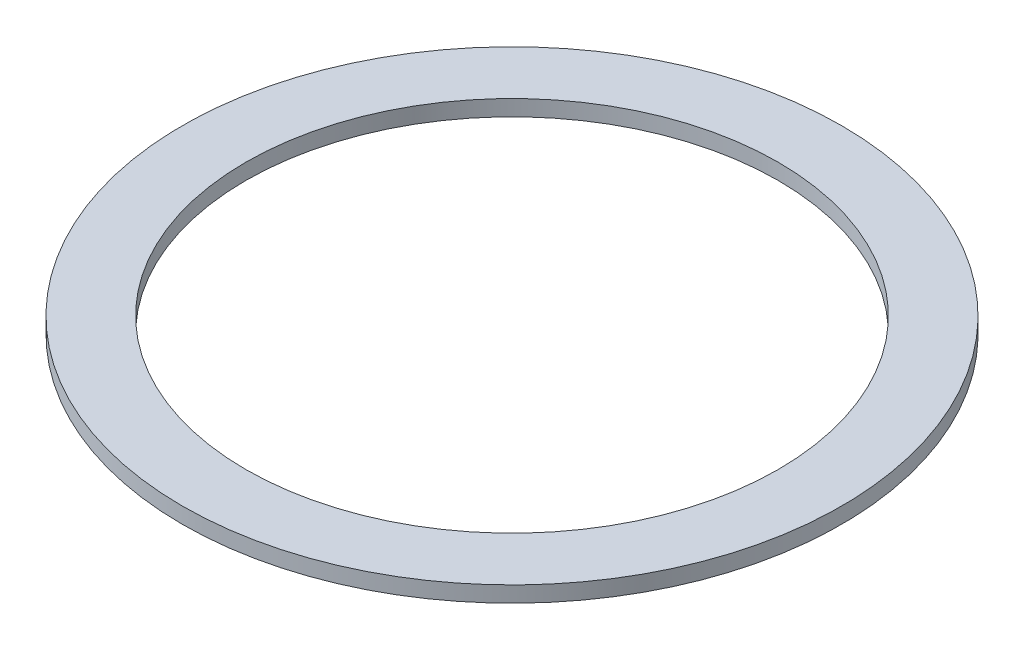
SolidWorks part; units mm, degrees
ref_plane "Front Plane" through (0, 0, 0) normal (0, 0, 1) x (1, 0, 0)
ref_plane "Top Plane" through (0, 0, 0) normal (0, 1, 0) x (1, 0, 0)
ref_plane "Right Plane" through (0, 0, 0) normal (1, 0, 0) x (0, 0, -1)
sketch "Sketch1" plane through (0, 0, 0) normal (0, 1, 0) x (1, 0, 0)
  circle A0 centre (0, 0) radius 26.67
  circle A1 centre (0, 0) radius 33.02
  dimension "D1" = 53.34
  dimension "D2" = 66.04
extrude "Boss-Extrude1" add sketch "Sketch1" along normal blind 1.5875
equation "\"D1@Sketch1\"=2.1in"
equation "\"D2@Sketch1\"=2.6in"
